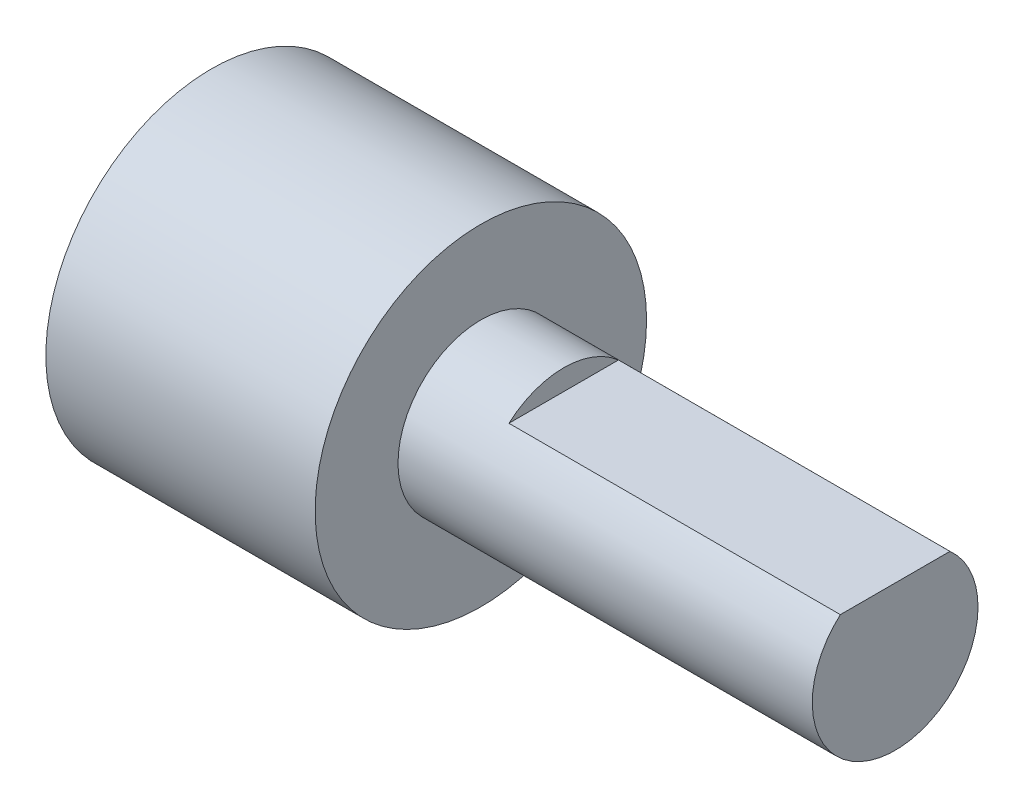
SolidWorks part; units mm, degrees
ref_plane "Plan de face" through (0, 0, 0) normal (0, 0, 1) x (1, 0, 0)
ref_plane "Plan de dessus" through (0, 0, 0) normal (0, 1, 0) x (1, 0, 0)
ref_plane "Plan de droite" through (0, 0, 0) normal (1, 0, 0) x (0, 0, -1)
sketch "Esquisse1" plane through (0, 0, 0) normal (1, 0, 0) x (0, 0, -1)
  circle A0 centre (0, 0) radius 4
  dimension "D1" = 8
extrude "Boss.-Extru.1" add sketch "Esquisse1" along normal blind 6.5
sketch "Esquisse2" plane through (6.5, 0, 0) normal (1, 0, 0) x (0, 0, -1)
  circle A0 centre (0, 0) radius 2
  dimension "D1" = 4
extrude "Boss.-Extru.2" add sketch "Esquisse2" along normal blind 10
sketch "Esquisse3" plane through (16.5, 0, 0) normal (1, 0, 0) x (0, 0, -1)
  line L1 (-2, 2) -> (2, 2)
  line L2 (-2, 2) -> (-2, 1.5)
  line L3 (-2, 1.5) -> (2, 1.5)
  line L4 (2, 2) -> (2, 1.5)
  dimension "D1" = 2
  dimension "D2" = 2
  dimension "D3" = 2
  dimension "D4" = 0.5
extrude "Enlèv. mat.-Extru.1" cut sketch "Esquisse3" against normal blind 8 contours L1 L4 L3 L2
